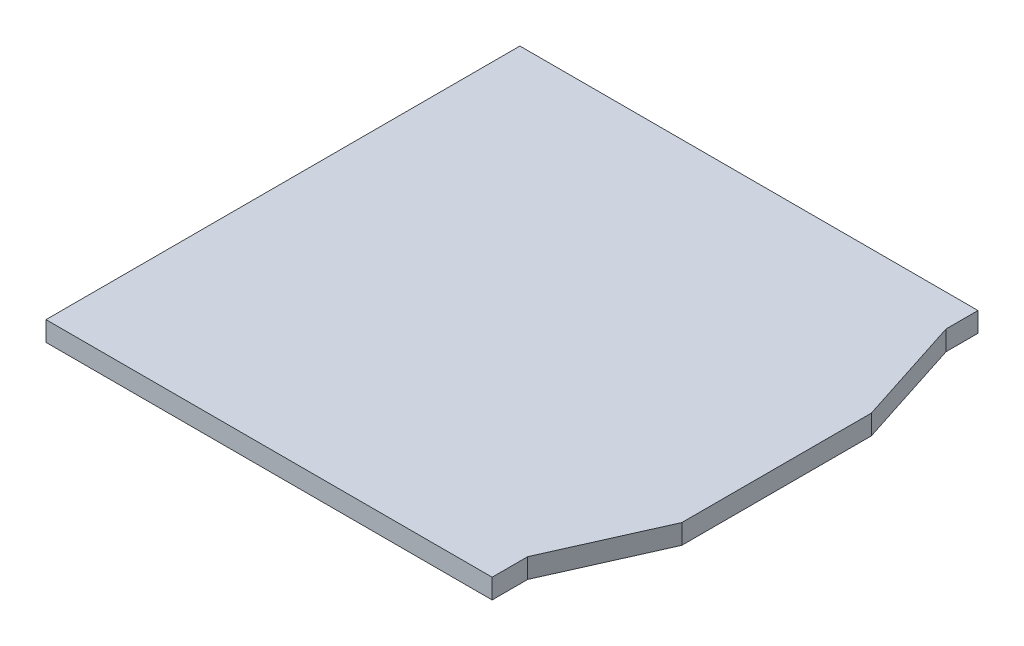
SolidWorks part; units mm, degrees
ref_plane "Front Plane" through (0, 0, 0) normal (0, 0, 1) x (1, 0, 0)
ref_plane "Top Plane" through (0, 0, 0) normal (0, 1, 0) x (1, 0, 0)
ref_plane "Right Plane" through (0, 0, 0) normal (1, 0, 0) x (0, 0, -1)
sketch "Sketch1" plane through (0, 0, 0) normal (0, 1, 0) x (1, 0, 0)
  line L0 (2.675, 3) -> (2.675, 2.5957)
  line L1 (-3.125, 3) -> (2.675, 3)
  line L2 (-3.125, 3) -> (-3.125, -3)
  line L3 (-3.125, -3) -> (2.5235, -3)
  line L4 (3.125, 1.2) -> (3.125, -1.2)
  line L5 (2.675, 2.5957) -> (3.125, 1.2)
  line L6 (2.5235, -3) -> (2.5235, -2.55)
  line L7 (2.5235, -2.55) -> (3.125, -1.2)
  point P4 (-3.125, 0)
  dimension "D1" = 0
  dimension "D2" = 6.25
  dimension "D4" = 6
  dimension "D5" = 0.45
  dimension "D6" = 1.8
  dimension "D7" = 1.8
  dimension "D8" = 0.45
extrude "Boss-Extrude1" add sketch "Sketch1" along normal blind 0.25 contours L4 L7 L6 L3 L2 L1 L0 L5
